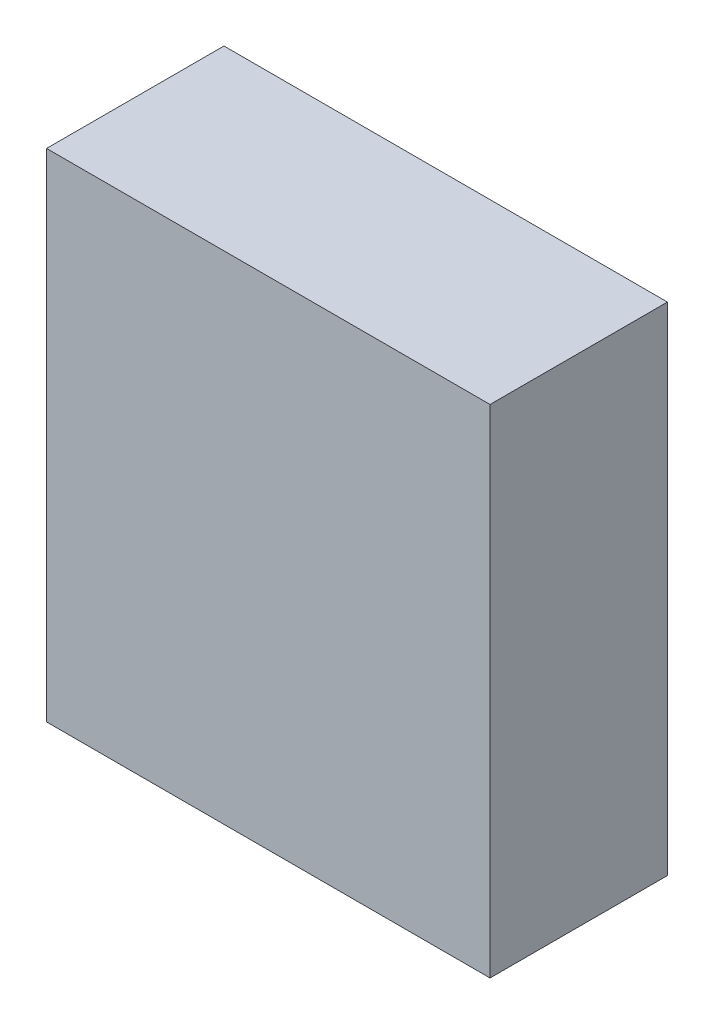
SolidWorks part; units mm, degrees
ref_plane "Front Plane" through (0, 0, 0) normal (0, 0, 1) x (1, 0, 0)
ref_plane "Top Plane" through (0, 0, 0) normal (0, 1, 0) x (1, 0, 0)
ref_plane "Right Plane" through (0, 0, 0) normal (1, 0, 0) x (0, 0, -1)
sketch "Sketch1" plane through (0, 0, 0) normal (0, 0, 1) x (1, 0, 0)
  line L1 (-125, -140) -> (125, -140)
  line L2 (-125, -140) -> (-125, 140)
  line L3 (-125, 140) -> (125, 140)
  line L4 (125, -140) -> (125, 140)
  line L5 (-125, -140) -> (125, 140) construction
  line L6 (-125, 140) -> (125, -140) construction
  point P0 (0, 0)
  dimension "D1" = 280
  dimension "D2" = 250
extrude "Boss-Extrude1" add sketch "Sketch1" along normal blind 100
